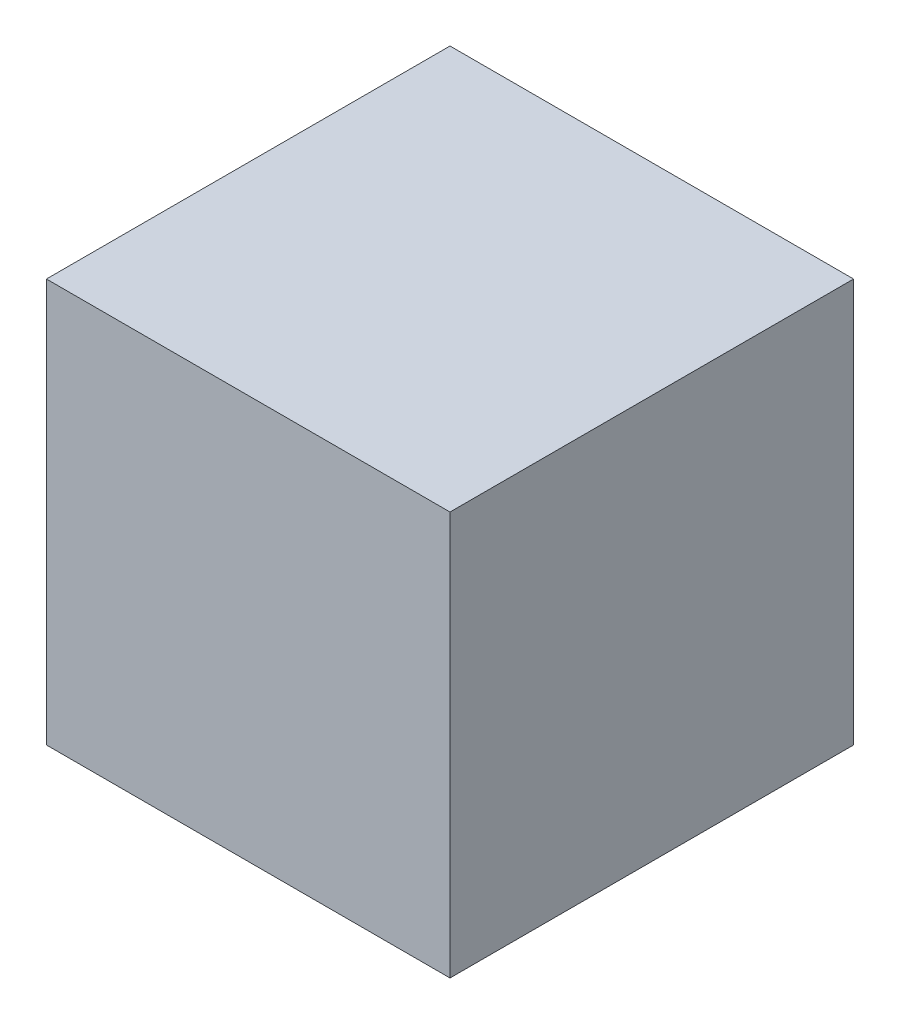
SolidWorks part; units mm, degrees
ref_plane "Front Plane" through (0, 0, 0) normal (0, 0, 1) x (1, 0, 0)
ref_plane "Top Plane" through (0, 0, 0) normal (0, 1, 0) x (1, 0, 0)
ref_plane "Right Plane" through (0, 0, 0) normal (1, 0, 0) x (0, 0, -1)
sketch "Sketch1" plane through (0, 0, 0) normal (0, 0, 1) x (1, 0, 0)
  line L1 (5, 5) -> (-5, 5)
  line L2 (5, 5) -> (5, -5)
  line L3 (5, -5) -> (-5, -5)
  line L4 (-5, 5) -> (-5, -5)
  line L5 (5, 5) -> (-5, -5) construction
  line L6 (5, -5) -> (-5, 5) construction
  point P0 (0, 0)
  dimension "D1" = 10
  dimension "D2" = 10
extrude "Boss-Extrude1" add sketch "Sketch1" along normal blind 10
sketch "Sketch2" plane through (0, 0, 10) normal (0, 0, 1) x (1, 0, 0)
  line L0 (5, 0) -> (-5, 0)
  line L1 (-5, 5) -> (-5, -5) construction
  point P6 (0, 0)
sketch "Sketch3" plane through (0, 0, 0) normal (0, 0, -1) x (-1, 0, 0)
  line L0 (0, 0) -> (12, 0) construction
  circle A0 centre (0, 0) radius 12
  dimension "D1" = 24
sketch "Sketch5" plane through (-5, 0, 0) normal (-1, 0, 0) x (0, 0, 1)
  line L0 (15, 0) -> (5, 0)
  line L2 (16.3121, 0) -> (16.3121, -2.3589)
  line L3 (16.3121, -2.3589) -> (15.8543, -1.5627)
  line L4 (16.3121, -2.3589) -> (16.7699, -1.5627)
  line L5 (16.7699, -1.5627) -> (15.8543, -1.5627) construction
  line L6 (16.3121, -2.7338) -> (16.3121, -3.4014)
  line L7 (16.6459, -3.0676) -> (15.9783, -3.0676)
  point P4 (10, 0)
  point P13 (16.3121, -1.5627)
  point P14 (16.3121, -3.0676)
  point P17 (16.3121, -3.0676)
  dimension "D1" = 10
